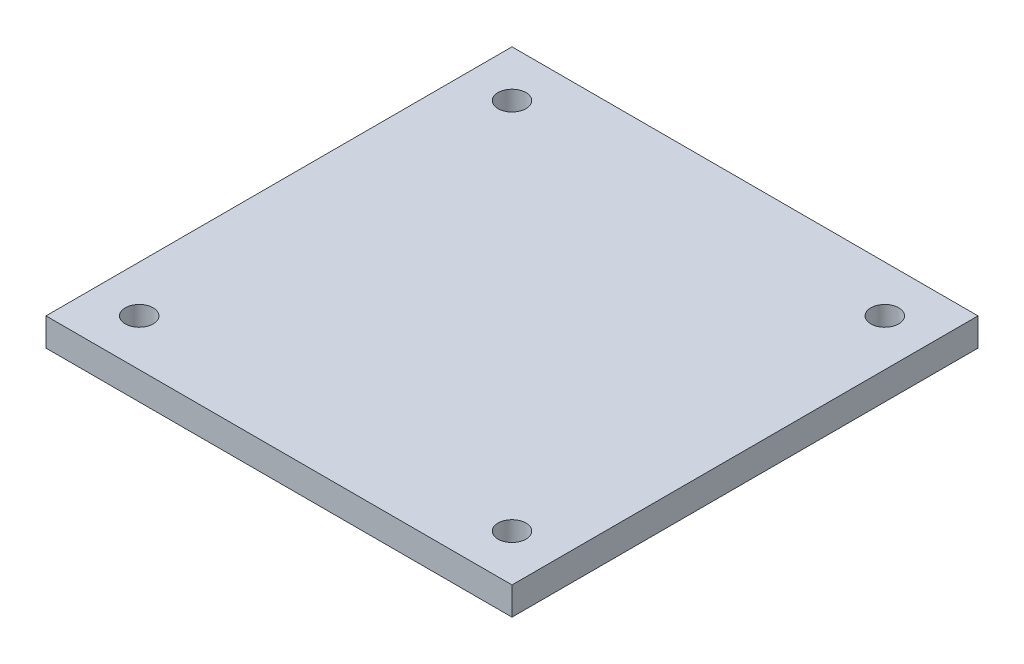
SolidWorks part; units mm, degrees
material "Copper"
ref_plane "Front Plane" through (0, 0, 0) normal (0, 0, 1) x (1, 0, 0)
ref_plane "Top Plane" through (0, 0, 0) normal (0, 1, 0) x (1, 0, 0)
ref_plane "Right Plane" through (0, 0, 0) normal (1, 0, 0) x (0, 0, -1)
sketch "Sketch1" plane through (0, 0, 0) normal (0, 1, 0) x (1, 0, 0)
  line L0 (0, 0) -> (0, 8.1284) construction
  line L1 (-25, 25) -> (25, 25)
  line L2 (-25, 25) -> (-25, -25)
  line L3 (-25, -25) -> (25, -25)
  line L4 (25, 25) -> (25, -25)
  line L5 (0, 0) -> (10.615, 0) construction
  circle A0 centre (20, 20) radius 1.5
  circle A4 centre (-20, 20) radius 1.5
  circle A5 centre (20, -20) radius 1.5
  circle A6 centre (-20, -20) radius 1.5
  dimension "D3" = 3
  dimension "D1" = 50
  dimension "D2" = 25
  dimension "D4" = 5
  dimension "D5" = 5
  dimension "D6" = 25
extrude "Boss-Extrude1" add sketch "Sketch1" along normal blind 3
